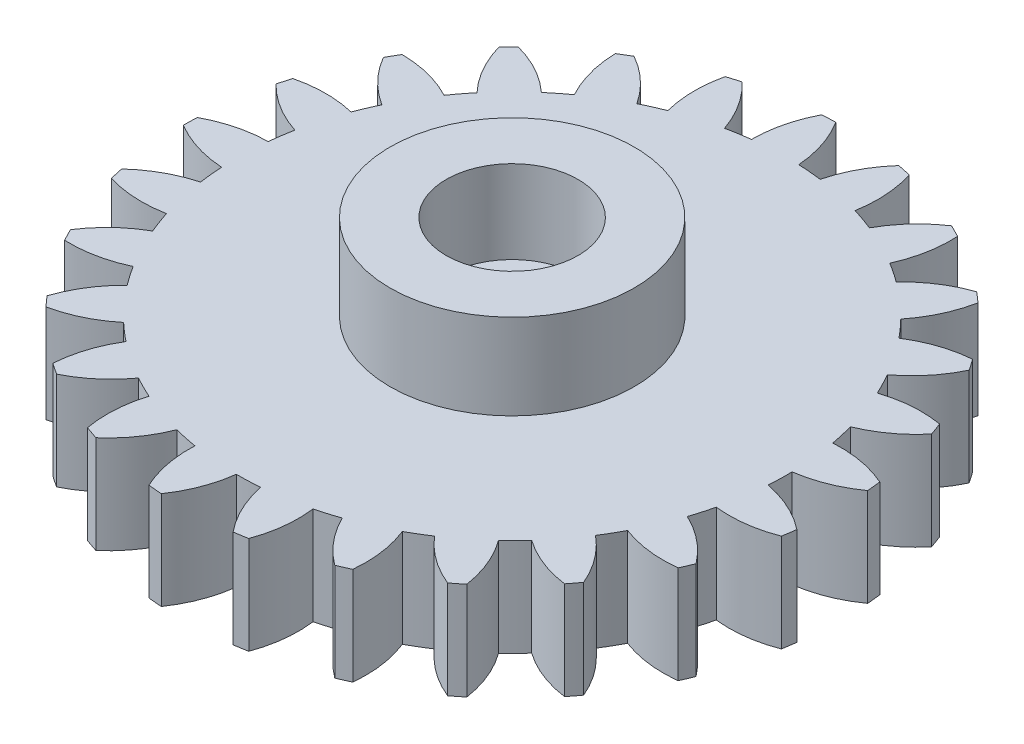
SolidWorks part; units mm, degrees
ref_plane "Front Plane" through (0, 0, 0) normal (0, 0, 1) x (1, 0, 0)
ref_plane "Top Plane" through (0, 0, 0) normal (0, 1, 0) x (1, 0, 0)
ref_plane "Right Plane" through (0, 0, 0) normal (1, 0, 0) x (0, 0, -1)
sketch "Sketch1" plane through (0, 0, 0) normal (0, 1, 0) x (1, 0, 0)
  arc A0 (3.9012, 14.0387) -> (3.745, 16.4117) centre (-1.023, 14.9062) ccw
  arc A1 (3.745, 16.4117) -> (3.1985, 16.5295) centre (0.6274, 3.2766) ccw
  arc A2 (3.1985, 16.5295) -> (2.0785, 14.4316) centre (6.9227, 13.1933) ccw
  arc A3 (2.0785, 14.4316) -> (1.1219, 14.5147) centre (0.6274, 3.2766) ccw
  arc A4 (1.1219, 14.5147) -> (0.3805, 16.7743) centre (-3.8633, 14.1304) ccw
  arc A5 (0.3805, 16.7743) -> (-0.1781, 16.7525) centre (0.6274, 3.2766) ccw
  arc A6 (-0.1781, 16.7525) -> (-0.7412, 14.442) centre (4.2588, 14.4474) ccw
  arc A7 (-0.7412, 14.442) -> (-1.6884, 14.2846) centre (0.6274, 3.2766) ccw
  arc A8 (-1.6884, 14.2846) -> (-2.9685, 16.2889) centre (-6.4214, 12.6726) ccw
  arc A9 (-2.9685, 16.2889) -> (-3.5041, 16.1288) centre (0.6274, 3.2766) ccw
  arc A10 (-3.5041, 16.1288) -> (-3.4749, 13.7509) centre (1.3666, 14.9995) ccw
  arc A11 (-3.4749, 13.7509) -> (-4.3532, 13.3629) centre (0.6274, 3.2766) ccw
  arc A12 (-4.3532, 13.3629) -> (-6.0915, 14.9858) centre (-8.5367, 10.6245) ccw
  arc A13 (-6.0915, 14.9858) -> (-6.5706, 14.6976) centre (0.6274, 3.2766) ccw
  arc A14 (-6.5706, 14.6976) -> (-5.9509, 12.4016) centre (-1.5719, 14.815) ccw
  arc A15 (-5.9509, 12.4016) -> (-6.7051, 11.8073) centre (0.6274, 3.2766) ccw
  arc A16 (-6.7051, 11.8073) -> (-8.7924, 12.947) centre (-10.0761, 8.1146) ccw
  arc A17 (-8.7924, 12.947) -> (-9.1847, 12.5487) centre (0.6274, 3.2766) ccw
  arc A18 (-9.1847, 12.5487) -> (-8.0135, 10.4789) centre (-4.3723, 13.9055) ccw
  arc A19 (-8.0135, 10.4789) -> (-8.5963, 9.7158) centre (0.6274, 3.2766) ccw
  arc A20 (-8.5963, 9.7158) -> (-10.9014, 10.3006) centre (-10.943, 5.3007) ccw
  arc A21 (-10.9014, 10.3006) -> (-11.1823, 9.8172) centre (0.6274, 3.2766) ccw
  arc A22 (-11.1823, 9.8172) -> (-9.5332, 8.1037) centre (-6.8586, 12.3282) ccw
  arc A23 (-9.5332, 8.1037) -> (-9.9078, 7.2197) centre (0.6274, 3.2766) ccw
  arc A24 (-9.9078, 7.2197) -> (-12.286, 7.2128) centre (-11.0829, 2.3597) ccw
  arc A25 (-12.286, 7.2128) -> (-12.4379, 6.6748) centre (0.6274, 3.2766) ccw
  arc A26 (-12.4379, 6.6748) -> (-10.4144, 5.4252) centre (-8.8744, 10.1822) ccw
  arc A27 (-10.4144, 5.4252) -> (-10.5575, 4.4758) centre (0.6274, 3.2766) ccw
  arc A28 (-10.5575, 4.4758) -> (-12.8592, 3.8777) centre (-10.4869, -0.5237) ccw
  arc A29 (-12.8592, 3.8777) -> (-12.8725, 3.3188) centre (0.6274, 3.2766) ccw
  arc A30 (-12.8725, 3.3188) -> (-10.6019, 2.6117) centre (-10.2932, 7.6022) ccw
  arc A31 (-10.6019, 2.6117) -> (-10.5043, 1.6565) centre (0.6274, 3.2766) ccw
  arc A32 (-10.5043, 1.6565) -> (-12.5849, 0.5048) centre (-9.1927, -3.1684) ccw
  arc A33 (-12.5849, 0.5048) -> (-12.4589, -0.0398) centre (0.6274, 3.2766) ccw
  arc A34 (-12.4589, -0.0398) -> (-10.0837, -0.16) centre (-11.0259, 4.7504) ccw
  arc A35 (-10.0837, -0.16) -> (-9.7517, -1.0609) centre (0.6274, 3.2766) ccw
  arc A36 (-9.7517, -1.0609) -> (-11.4805, -2.6939) centre (-7.2813, -5.4081) ccw
  arc A37 (-11.4805, -2.6939) -> (-11.223, -3.1901) centre (0.6274, 3.2766) ccw
  arc A38 (-11.223, -3.1901) -> (-8.8926, -2.7158) centre (-11.0263, 1.8061) ccw
  arc A39 (-8.8926, -2.7158) -> (-8.3469, -3.5058) centre (0.6274, 3.2766) ccw
  arc A40 (-8.3469, -3.5058) -> (-9.6153, -5.5174) centre (-4.8731, -7.1021) ccw
  arc A41 (-9.6153, -5.5174) -> (-9.2425, -5.934) centre (0.6274, 3.2766) ccw
  arc A42 (-9.2425, -5.934) -> (-7.1032, -4.8951) centre (-10.2945, -1.0459) ccw
  arc A43 (-7.1032, -4.8951) -> (-6.3782, -5.5246) centre (0.6274, 3.2766) ccw
  arc A44 (-6.3782, -5.5246) -> (-7.1066, -7.7884) centre (-2.1192, -8.1439) ccw
  arc A45 (-7.1066, -7.7884) -> (-6.6418, -8.0992) centre (0.6274, 3.2766) ccw
  arc A46 (-6.6418, -8.0992) -> (-4.8282, -6.5609) centre (-8.8764, -3.6263) ccw
  arc A47 (-4.8282, -6.5609) -> (-3.9693, -6.9903) centre (0.6274, 3.2766) ccw
  arc A48 (-3.9693, -6.9903) -> (-4.1118, -9.3642) centre (0.8073, -8.4682) ccw
  arc A49 (-4.1118, -9.3642) -> (-3.5844, -9.5496) centre (0.6274, 3.2766) ccw
  arc A50 (-3.5844, -9.5496) -> (-2.2103, -7.6086) centre (-6.8611, -5.7729) ccw
  arc A51 (-2.2103, -7.6086) -> (-1.2717, -7.8109) centre (0.6274, 3.2766) ccw
  arc A52 (-1.2717, -7.8109) -> (-0.8193, -10.1457) centre (3.7224, -8.0545) ccw
  arc A53 (-0.8193, -10.1457) -> (-0.2623, -10.194) centre (0.6274, 3.2766) ccw
  arc A54 (-0.2623, -10.194) -> (0.5859, -7.9723) centre (-4.3753, -7.3509) ccw
  arc A55 (0.5859, -7.9723) -> (1.5454, -7.9349) centre (0.6274, 3.2766) ccw
  arc A56 (1.5454, -7.9349) -> (2.5642, -10.0838) centre (6.4431, -6.9288) ccw
  arc A57 (2.5642, -10.0838) -> (3.1156, -9.9921) centre (0.6274, 3.2766) ccw
  arc A58 (3.1156, -9.9921) -> (3.3847, -7.6292) centre (-1.5752, -8.2612) ccw
  arc A59 (3.3847, -7.6292) -> (4.3047, -7.3544) centre (0.6274, 3.2766) ccw
  arc A60 (4.3047, -7.3544) -> (5.8259, -9.1824) centre (8.7984, -5.1619) ccw
  arc A61 (5.8259, -9.1824) -> (6.3373, -8.9565) centre (0.6274, 3.2766) ccw
  arc A62 (6.3373, -8.9565) -> (6.0103, -6.6009) centre (1.3634, -8.4465) ccw
  arc A63 (6.0103, -6.6009) -> (6.833, -6.1059) centre (0.6274, 3.2766) ccw
  arc A64 (6.833, -6.1059) -> (8.761, -7.4982) centre (10.6402, -2.8648) ccw
  arc A65 (8.761, -7.4982) -> (9.2001, -7.1522) centre (0.6274, 3.2766) ccw
  arc A66 (9.2001, -7.1522) -> (8.2976, -4.9519) centre (4.2556, -7.8952) ccw
  arc A67 (8.2976, -4.9519) -> (8.9714, -4.2679) centre (0.6274, 3.2766) ccw
  arc A68 (8.9714, -4.2679) -> (11.185, -5.1369) centre (11.853, -0.1817) ccw
  arc A69 (11.185, -5.1369) -> (11.5243, -4.6926) centre (0.6274, 3.2766) ccw
  arc A70 (11.5243, -4.6926) -> (10.103, -2.7859) centre (6.92, -6.6419) ccw
  arc A71 (10.103, -2.7859) -> (10.5855, -1.9558) centre (0.6274, 3.2766) ccw
  arc A72 (10.5855, -1.9558) -> (12.9457, -2.247) centre (12.3603, 2.7186) ccw
  arc A73 (12.9457, -2.247) -> (13.1638, -1.7323) centre (0.6274, 3.2766) ccw
  arc A74 (13.1638, -1.7323) -> (11.313, -0.239) centre (9.1889, -4.7654) ccw
  arc A75 (11.313, -0.239) -> (11.5739, 0.6851) centre (0.6274, 3.2766) ccw
  arc A76 (11.5739, 0.6851) -> (13.9324, 0.9899) centre (12.1305, 5.654) ccw
  arc A77 (13.9324, 0.9899) -> (14.0156, 1.5428) centre (0.6274, 3.2766) ccw
  arc A78 (14.0156, 1.5428) -> (11.8516, 2.5288) centre (10.9199, -2.3836) ccw
  arc A79 (11.8516, 2.5288) -> (11.8744, 3.4887) centre (0.6274, 3.2766) ccw
  arc A80 (11.8744, 3.4887) -> (14.083, 4.3706) centre (11.1779, 8.44) ccw
  arc A81 (14.083, 4.3706) -> (14.0262, 4.9267) centre (0.6274, 3.2766) ccw
  arc A82 (14.0262, 4.9267) -> (11.6849, 5.3437) centre (12.0042, 0.3539) ccw
  arc A83 (11.6849, 5.3437) -> (11.4683, 6.2791) centre (0.6274, 3.2766) ccw
  arc A84 (11.4683, 6.2791) -> (13.3883, 7.6825) centre (9.5623, 10.9015) ccw
  arc A85 (13.3883, 7.6825) -> (13.1949, 8.207) centre (0.6274, 3.2766) ccw
  arc A86 (13.1949, 8.207) -> (10.8235, 8.0286) centre (12.3736, 3.275) ccw
  arc A87 (10.8235, 8.0286) -> (10.3811, 8.8808) centre (0.6274, 3.2766) ccw
  arc A88 (10.3811, 8.8808) -> (11.8917, 10.7175) centre (7.3854, 12.884) ccw
  arc A89 (11.8917, 10.7175) -> (11.5739, 11.1775) centre (0.6274, 3.2766) ccw
  arc A90 (11.5739, 11.1775) -> (9.3214, 10.4149) centre (12.005, 6.1962) ccw
  arc A91 (9.3214, 10.4149) -> (8.6809, 11.1303) centre (0.6274, 3.2766) ccw
  arc A92 (8.6809, 11.1303) -> (9.6873, 13.2851) centre (4.7838, 14.2628) ccw
  arc A93 (9.6873, 13.2851) -> (9.2651, 13.6516) centre (0.6274, 3.2766) ccw
  arc A94 (9.2651, 13.6516) -> (7.273, 12.3528) centre (10.9215, 8.9339) ccw
  arc A95 (7.273, 12.3528) -> (6.4748, 12.8864) centre (0.6274, 3.2766) ccw
  arc A96 (6.4748, 12.8864) -> (6.9136, 15.2237) centre (1.9211, 14.9513) ccw
  arc A97 (6.9136, 15.2237) -> (6.4136, 15.4737) centre (0.6274, 3.2766) ccw
  arc A98 (6.4136, 15.4737) -> (4.8071, 13.7203) centre (9.1912, 11.3162) ccw
  arc A99 (4.8071, 13.7203) -> (3.9012, 14.0387) centre (0.6274, 3.2766) ccw
extrude "Boss-Extrude1" add sketch "Sketch1" along normal blind 4
sketch "Sketch2" plane through (0, 4, 0) normal (0, 1, 0) x (1, 0, 0)
  circle A2 centre (0.6274, 3.2766) radius 11.249 construction
  circle A4 centre (0.6274, 3.2766) radius 5
  dimension "D1" = 10
extrude "Boss-Extrude2" add sketch "Sketch2" along normal blind 3.5
sketch "Sketch3" plane through (0, 7.5, 0) normal (0, 1, 0) x (1, 0, 0)
  circle A0 centre (0.6274, 3.2766) radius 2.7
  dimension "D1" = 5.4
extrude "Cut-Extrude1" cut sketch "Sketch3" against normal blind 3.4
sketch "Sketch4" plane through (0, 0, 0) normal (0, -1, 0) x (1, 0, 0)
  circle A0 centre (0.6274, -3.2766) radius 5 construction
  circle A1 centre (0.6274, -3.2766) radius 5 construction
  circle A2 centre (0.6274, -3.2766) radius 2.35
  dimension "D1" = 4.7
extrude "Cut-Extrude2" cut sketch "Sketch4" against normal blind 1.5
